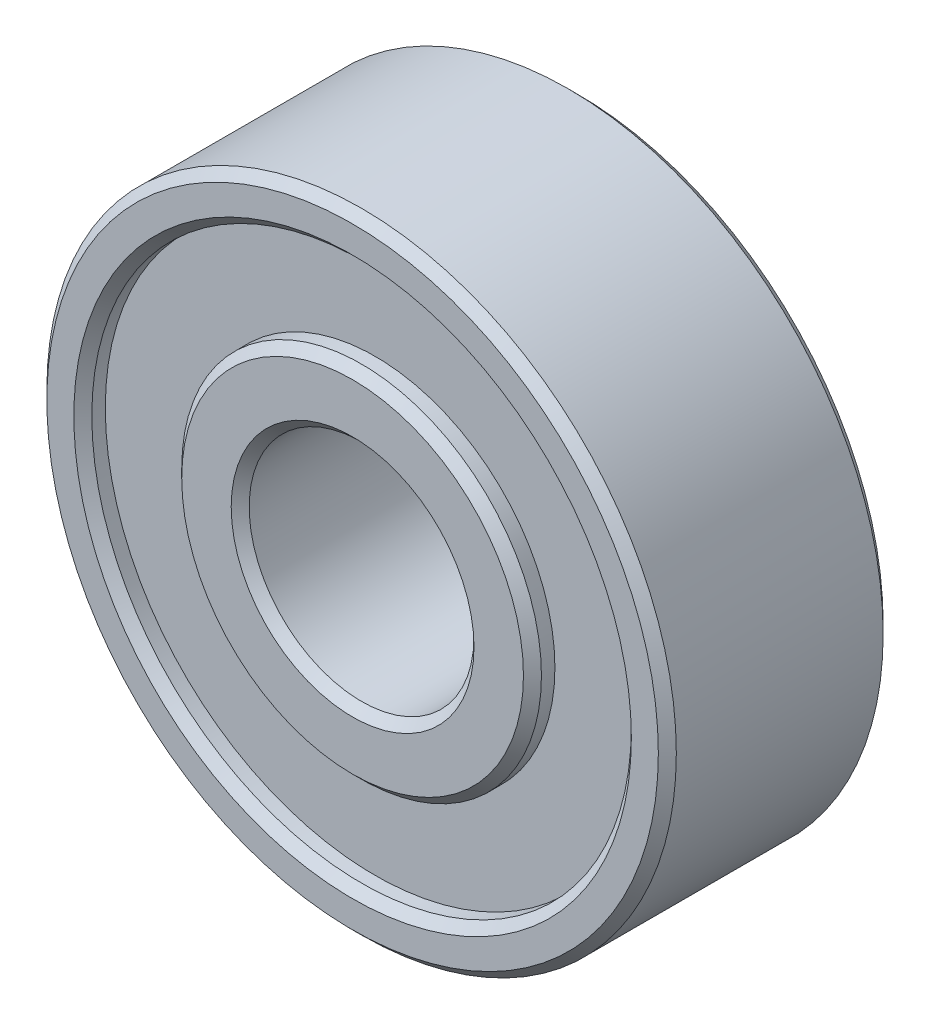
SolidWorks part; units mm, degrees
material "1.4307 (X2CrNi18-9)"
ref_plane "Alzado" through (0, 0, 0) normal (0, 0, 1) x (1, 0, 0)
ref_plane "Planta" through (0, 0, 0) normal (0, 1, 0) x (1, 0, 0)
ref_plane "Vista lateral" through (0, 0, 0) normal (1, 0, 0) x (0, 0, -1)
sketch "Croquis1" plane through (0, 0, 0) normal (0, 0, 1) x (1, 0, 0)
  circle A0 centre (0, 0) radius 7
  dimension "D1" = 14
extrude "Saliente-Extruir1" add sketch "Croquis1" along normal blind 5
sketch "Croquis2" plane through (0, 0, 5) normal (0, 0, 1) x (1, 0, 0)
  circle A0 centre (0, 0) radius 2.5
extrude "Cortar-Extruir1" cut sketch "Croquis2" against normal blind 5
sketch "Croquis3" plane through (0, 0, 5) normal (0, 0, 1) x (1, 0, 0)
  circle A0 centre (0, 0) radius 4
  circle A1 centre (0, 0) radius 6
extrude "Cortar-Extruir3" cut sketch "Croquis3" against normal blind 0.5
sketch "Croquis4" plane through (0, 0, 0) normal (0, 0, -1) x (-1, 0, 0)
  circle A0 centre (0, 0) radius 4
  circle A1 centre (0, 0) radius 6
extrude "Cortar-Extruir4" cut sketch "Croquis4" against normal blind 0.5
chamfer "Chaflán1" distance 0.2 angle 45 8 edges at (-6, 0, 0) (-4, 0, 0) (6, 0, 5) (4, 0, 5) (2.5, 0, 5) (2.5, 0, 0) (7, 0, 0) (7, 0, 5)
sketch "Croquis5" plane through (0, 0, 5) normal (0, 0, 1) x (1, 0, 0)
